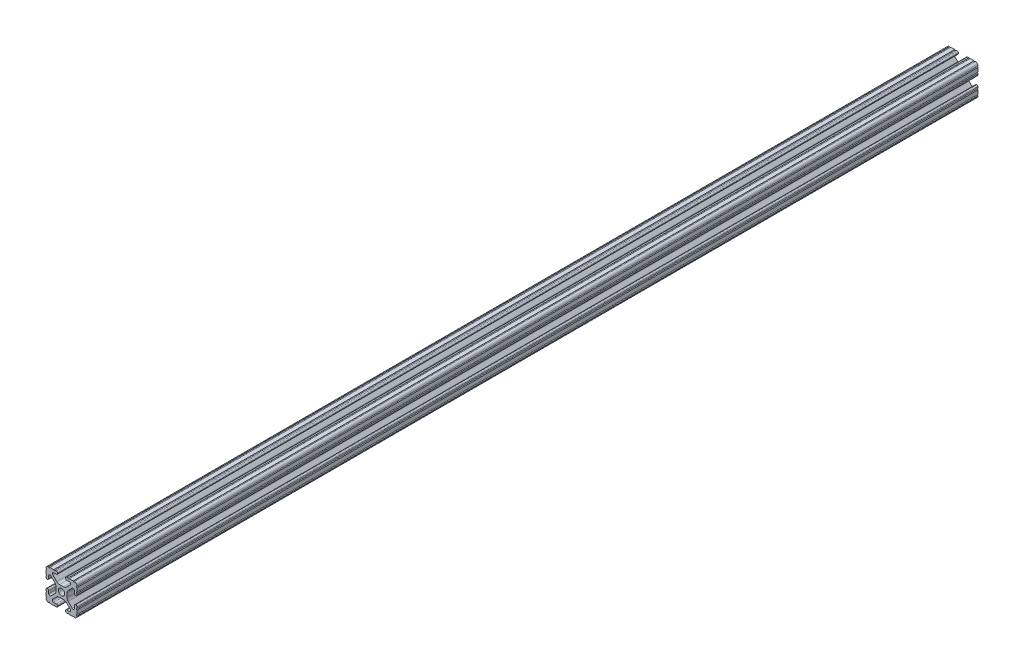
SolidWorks part; units mm, degrees
ref_plane "Front Plane" through (0, 0, 0) normal (0, 0, 1) x (1, 0, 0)
ref_plane "Top Plane" through (0, 0, 0) normal (0, 1, 0) x (1, 0, 0)
ref_plane "Right Plane" through (0, 0, 0) normal (1, 0, 0) x (0, 0, -1)
sketch "Sketch1" plane through (0, 0, 0) normal (0, 0, 1) x (1, 0, 0)
  line L88 (-7.1797, -8.6452) -> (-3.9523, -5.4237)
  line L89 (-1.7093, -4.4958) -> (1.7093, -4.4958)
  line L90 (3.9523, -5.4237) -> (7.1797, -8.6452)
  line L91 (6.4164, -10.4902) -> (4.2875, -10.4902)
  line L92 (3.2385, -11.5392) -> (3.2385, -11.651)
  line L93 (4.2875, -12.7) -> (5.3171, -12.7)
  line L94 (6.3331, -12.7) -> (9.5504, -12.7)
  line L95 (12.7, -9.5504) -> (12.7, -6.3331)
  line L96 (12.7, -5.3171) -> (12.7, -4.2875)
  line L97 (11.651, -3.2385) -> (11.5392, -3.2385)
  line L98 (10.4902, -4.2875) -> (10.4902, -6.4021)
  line L99 (8.7371, -7.1294) -> (5.441, -3.8408)
  line L100 (4.5085, -1.5932) -> (4.5085, 1.5932)
  line L101 (5.441, 3.8408) -> (8.7371, 7.1294)
  line L102 (10.4902, 6.4021) -> (10.4902, 4.2875)
  line L103 (11.5392, 3.2385) -> (11.651, 3.2385)
  line L104 (12.7, 4.2875) -> (12.7, 5.3171)
  line L105 (12.7, 6.3331) -> (12.7, 9.5504)
  line L106 (9.5504, 12.7) -> (6.3331, 12.7)
  line L107 (5.3171, 12.7) -> (4.2875, 12.7)
  line L108 (3.2385, 11.651) -> (3.2385, 11.5392)
  line L109 (4.2875, 10.4902) -> (6.4768, 10.4902)
  line L110 (7.207, 8.7244) -> (3.8983, 5.4232)
  line L111 (1.6558, 4.4958) -> (-1.6558, 4.4958)
  line L112 (-3.8983, 5.4232) -> (-7.207, 8.7244)
  line L113 (-6.4768, 10.4902) -> (-4.2875, 10.4902)
  line L114 (-3.2385, 11.5392) -> (-3.2385, 11.651)
  line L115 (-4.2875, 12.7) -> (-5.3171, 12.7)
  line L116 (-6.3331, 12.7) -> (-9.5504, 12.7)
  line L117 (-12.7, 9.5504) -> (-12.7, 6.3331)
  line L118 (-12.7, 5.3171) -> (-12.7, 4.2875)
  line L119 (-11.651, 3.2385) -> (-11.5392, 3.2385)
  line L120 (-10.4902, 4.2875) -> (-10.4902, 6.4021)
  line L121 (-8.7371, 7.1294) -> (-5.441, 3.8408)
  line L122 (-4.5085, 1.5932) -> (-4.5085, -1.5932)
  line L123 (-5.441, -3.8408) -> (-8.7371, -7.1294)
  line L124 (-10.4902, -6.4021) -> (-10.4902, -4.2875)
  line L125 (-11.5392, -3.2385) -> (-11.651, -3.2385)
  line L126 (-12.7, -4.2875) -> (-12.7, -5.3171)
  line L127 (-12.7, -6.3331) -> (-12.7, -9.5504)
  line L128 (-9.5504, -12.7) -> (-6.3331, -12.7)
  line L129 (-5.3171, -12.7) -> (-4.2875, -12.7)
  line L130 (-3.2385, -11.651) -> (-3.2385, -11.5392)
  line L131 (-4.2875, -10.4902) -> (-6.4164, -10.4902)
  circle A1 centre (0, 0) radius 2.6035
  arc A104 (-7.1797, -8.6452) -> (-6.4164, -10.4902) centre (-6.4164, -9.4098) ccw
  arc A105 (-1.7093, -4.4958) -> (-3.9523, -5.4237) centre (-1.7093, -7.6708) ccw
  arc A106 (3.9523, -5.4237) -> (1.7093, -4.4958) centre (1.7093, -7.6708) ccw
  arc A107 (6.4164, -10.4902) -> (7.1797, -8.6452) centre (6.4164, -9.4098) ccw
  arc A108 (4.2875, -10.4902) -> (3.2385, -11.5392) centre (4.2875, -11.5392) ccw
  arc A109 (3.2385, -11.651) -> (4.2875, -12.7) centre (4.2875, -11.651) ccw
  arc A110 (6.3331, -12.7) -> (5.3171, -12.7) centre (5.8251, -12.7) ccw
  arc A111 (10.5664, -12.6998) -> (9.5504, -12.7) centre (10.0584, -12.7) ccw
  arc A112 (10.5664, -12.6998) -> (12.6998, -10.5664) centre (10.5918, -10.5918) ccw
  arc A113 (12.7, -9.5504) -> (12.6998, -10.5664) centre (12.7, -10.0584) ccw
  arc A114 (12.7, -5.3171) -> (12.7, -6.3331) centre (12.7, -5.8251) ccw
  arc A115 (12.7, -4.2875) -> (11.651, -3.2385) centre (11.651, -4.2875) ccw
  arc A116 (11.5392, -3.2385) -> (10.4902, -4.2875) centre (11.5392, -4.2875) ccw
  arc A117 (8.7371, -7.1294) -> (10.4902, -6.4021) centre (9.4628, -6.4021) ccw
  arc A118 (4.5085, -1.5932) -> (5.441, -3.8408) centre (7.6835, -1.5932) ccw
  arc A119 (5.441, 3.8408) -> (4.5085, 1.5932) centre (7.6835, 1.5932) ccw
  arc A120 (10.4902, 6.4021) -> (8.7371, 7.1294) centre (9.4628, 6.4021) ccw
  arc A121 (10.4902, 4.2875) -> (11.5392, 3.2385) centre (11.5392, 4.2875) ccw
  arc A122 (11.651, 3.2385) -> (12.7, 4.2875) centre (11.651, 4.2875) ccw
  arc A123 (12.7, 6.3331) -> (12.7, 5.3171) centre (12.7, 5.8251) ccw
  arc A124 (12.6998, 10.5664) -> (12.7, 9.5504) centre (12.7, 10.0584) ccw
  arc A125 (12.6998, 10.5664) -> (10.5664, 12.6998) centre (10.5918, 10.5918) ccw
  arc A126 (9.5504, 12.7) -> (10.5664, 12.6998) centre (10.0584, 12.7) ccw
  arc A127 (5.3171, 12.7) -> (6.3331, 12.7) centre (5.8251, 12.7) ccw
  arc A128 (4.2875, 12.7) -> (3.2385, 11.651) centre (4.2875, 11.651) ccw
  arc A129 (3.2385, 11.5392) -> (4.2875, 10.4902) centre (4.2875, 11.5392) ccw
  arc A130 (7.207, 8.7244) -> (6.4768, 10.4902) centre (6.4768, 9.4563) ccw
  arc A131 (1.6558, 4.4958) -> (3.8983, 5.4232) centre (1.6558, 7.6708) ccw
  arc A132 (-3.8983, 5.4232) -> (-1.6558, 4.4958) centre (-1.6558, 7.6708) ccw
  arc A133 (-6.4768, 10.4902) -> (-7.207, 8.7244) centre (-6.4768, 9.4563) ccw
  arc A134 (-4.2875, 10.4902) -> (-3.2385, 11.5392) centre (-4.2875, 11.5392) ccw
  arc A135 (-3.2385, 11.651) -> (-4.2875, 12.7) centre (-4.2875, 11.651) ccw
  arc A136 (-6.3331, 12.7) -> (-5.3171, 12.7) centre (-5.8251, 12.7) ccw
  arc A137 (-10.5664, 12.6998) -> (-9.5504, 12.7) centre (-10.0584, 12.7) ccw
  arc A138 (-10.5664, 12.6998) -> (-12.6998, 10.5664) centre (-10.5918, 10.5918) ccw
  arc A139 (-12.7, 9.5504) -> (-12.6998, 10.5664) centre (-12.7, 10.0584) ccw
  arc A140 (-12.7, 5.3171) -> (-12.7, 6.3331) centre (-12.7, 5.8251) ccw
  arc A141 (-12.7, 4.2875) -> (-11.651, 3.2385) centre (-11.651, 4.2875) ccw
  arc A142 (-11.5392, 3.2385) -> (-10.4902, 4.2875) centre (-11.5392, 4.2875) ccw
  arc A143 (-8.7371, 7.1294) -> (-10.4902, 6.4021) centre (-9.4628, 6.4021) ccw
  arc A144 (-4.5085, 1.5932) -> (-5.441, 3.8408) centre (-7.6835, 1.5932) ccw
  arc A145 (-5.441, -3.8408) -> (-4.5085, -1.5932) centre (-7.6835, -1.5932) ccw
  arc A146 (-10.4902, -6.4021) -> (-8.7371, -7.1294) centre (-9.4628, -6.4021) ccw
  arc A147 (-10.4902, -4.2875) -> (-11.5392, -3.2385) centre (-11.5392, -4.2875) ccw
  arc A148 (-11.651, -3.2385) -> (-12.7, -4.2875) centre (-11.651, -4.2875) ccw
  arc A149 (-12.7, -6.3331) -> (-12.7, -5.3171) centre (-12.7, -5.8251) ccw
  arc A150 (-12.6998, -10.5664) -> (-12.7, -9.5504) centre (-12.7, -10.0584) ccw
  arc A151 (-12.6998, -10.5664) -> (-10.5664, -12.6998) centre (-10.5918, -10.5918) ccw
  arc A152 (-9.5504, -12.7) -> (-10.5664, -12.6998) centre (-10.0584, -12.7) ccw
  arc A153 (-5.3171, -12.7) -> (-6.3331, -12.7) centre (-5.8251, -12.7) ccw
  arc A154 (-4.2875, -12.7) -> (-3.2385, -11.651) centre (-4.2875, -11.651) ccw
  arc A155 (-3.2385, -11.5392) -> (-4.2875, -10.4902) centre (-4.2875, -11.5392) ccw
extrude "Boss-Extrude1" add sketch "Sketch1" along normal mid plane 736.6
